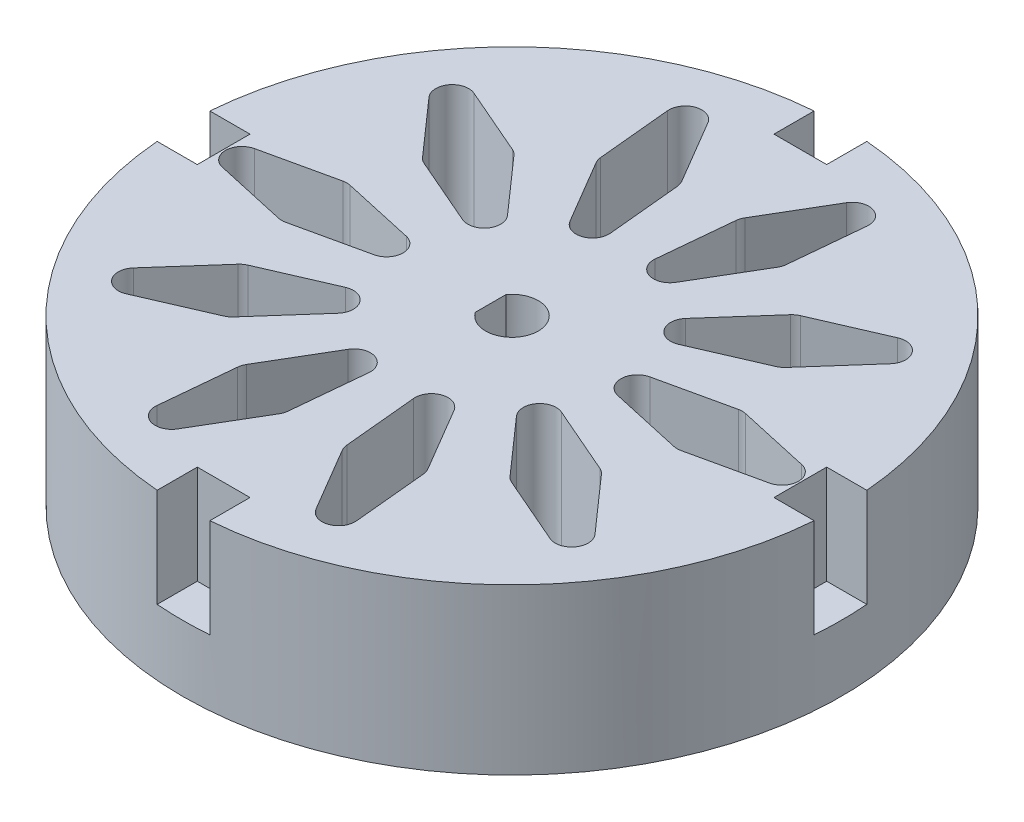
SolidWorks part; units mm, degrees
material "PET"
ref_plane "Спереди" through (0, 0, 0) normal (0, 0, 1) x (1, 0, 0)
ref_plane "Сверху" through (0, 0, 0) normal (0, 1, 0) x (1, 0, 0)
ref_plane "Справа" through (0, 0, 0) normal (1, 0, 0) x (0, 0, -1)
sketch "Эскиз1" plane through (0, 0, 0) normal (0, 1, 0) x (1, 0, 0)
  circle A0 centre (0, 0) radius 4
  circle A1 centre (0, 0) radius 20
  dimension "D1" = 8
  dimension "D2" = 40
extrude "Бобышка-Вытянуть1" add sketch "Эскиз1" along normal blind 10
sketch "Эскиз4" plane through (0, 0, 0) normal (0, -1, 0) x (1, 0, 0)
  circle A16 centre (0, 0) radius 20
  circle A32 centre (0, 0) radius 20
  dimension "D1" = 0
extrude "Бобышка-Вытянуть2" add sketch "Эскиз4" against normal blind 6
sketch "Эскиз5" plane through (0, 6, 0) normal (0, 1, 0) x (1, 0, 0)
  circle A0 centre (0, 0) radius 1.6
  dimension "D1" = 3.2
extrude "Вырез-Вытянуть2" cut sketch "Эскиз5" against normal through all both and the other way through all
sketch "Эскиз6" plane through (0, 0, 0) normal (0, -1, 0) x (1, 0, 0)
  line L0 (0, 0) -> (-3, 0) construction
  line L1 (-7.3928, 0.9762) -> (-11.7831, 1.9518)
  line L2 (-12.2169, 1.9518) -> (-16.6072, 0.9762)
  line L3 (-16.6072, -0.9762) -> (-12.2169, -1.9518)
  line L4 (-11.7831, -1.9518) -> (-7.3928, -0.9762)
  line L5 (-21, 0) -> (-3, 0) construction
  line L6 (-12, 2) -> (-12, -2) construction
  line L7 (-5.4071, 5.1352) -> (-8.3855, 8.5049)
  line L8 (-8.7365, 8.76) -> (-12.8617, 10.5512)
  line L9 (-14.0093, 8.9717) -> (-11.0309, 5.6019)
  line L10 (-10.6799, 5.3469) -> (-6.5547, 3.5557)
  line L11 (0, 0) -> (-2.4271, 1.7634) construction
  line L12 (-16.9894, 12.3435) -> (-2.4271, 1.7634) construction
  line L13 (-8.5326, 8.6715) -> (-10.8838, 5.4354) construction
  line L14 (-1.3561, 7.3327) -> (-1.7849, 11.8095)
  line L15 (-1.919, 12.2221) -> (-4.2035, 16.096)
  line L16 (-6.0603, 15.4927) -> (-5.6315, 11.0159)
  line L17 (-5.4974, 10.6032) -> (-3.2129, 6.7294)
  line L18 (0, 0) -> (-0.9271, 2.8532) construction
  line L19 (-6.4894, 19.9722) -> (-0.9271, 2.8532) construction
  line L20 (-1.8061, 12.0307) -> (-5.6103, 10.7946) construction
  line L21 (3.2129, 6.7294) -> (5.4974, 10.6032)
  line L22 (5.6315, 11.0159) -> (6.0603, 15.4927)
  line L23 (4.2035, 16.096) -> (1.919, 12.2221)
  line L24 (1.7849, 11.8095) -> (1.3561, 7.3327)
  line L25 (0, 0) -> (0.9271, 2.8532) construction
  line L26 (6.4894, 19.9722) -> (0.9271, 2.8532) construction
  line L27 (5.6103, 10.7946) -> (1.8061, 12.0307) construction
  line L28 (6.5547, 3.5557) -> (10.6799, 5.3469)
  line L29 (11.0309, 5.6019) -> (14.0093, 8.9717)
  line L30 (12.8617, 10.5512) -> (8.7365, 8.76)
  line L31 (8.3855, 8.5049) -> (5.4071, 5.1352)
  line L32 (0, 0) -> (2.4271, 1.7634) construction
  line L33 (16.9894, 12.3435) -> (2.4271, 1.7634) construction
  line L34 (10.8838, 5.4354) -> (8.5326, 8.6715) construction
  line L35 (7.3928, -0.9762) -> (11.7831, -1.9518)
  line L36 (12.2169, -1.9518) -> (16.6072, -0.9762)
  line L37 (16.6072, 0.9762) -> (12.2169, 1.9518)
  line L38 (11.7831, 1.9518) -> (7.3928, 0.9762)
  line L39 (0, 0) -> (3, 0) construction
  line L40 (21, 0) -> (3, 0) construction
  line L41 (12, -2) -> (12, 2) construction
  line L42 (5.4071, -5.1352) -> (8.3855, -8.5049)
  line L43 (8.7365, -8.76) -> (12.8617, -10.5512)
  line L44 (14.0093, -8.9717) -> (11.0309, -5.6019)
  line L45 (10.6799, -5.3469) -> (6.5547, -3.5557)
  line L46 (0, 0) -> (2.4271, -1.7634) construction
  line L47 (16.9894, -12.3435) -> (2.4271, -1.7634) construction
  line L48 (8.5326, -8.6715) -> (10.8838, -5.4354) construction
  line L49 (1.3561, -7.3327) -> (1.7849, -11.8095)
  line L50 (1.919, -12.2221) -> (4.2035, -16.096)
  line L51 (6.0603, -15.4927) -> (5.6315, -11.0159)
  line L52 (5.4974, -10.6032) -> (3.2129, -6.7294)
  line L53 (0, 0) -> (0.9271, -2.8532) construction
  line L54 (6.4894, -19.9722) -> (0.9271, -2.8532) construction
  line L55 (1.8061, -12.0307) -> (5.6103, -10.7946) construction
  line L56 (-3.2129, -6.7294) -> (-5.4974, -10.6032)
  line L57 (-5.6315, -11.0159) -> (-6.0603, -15.4927)
  line L58 (-4.2035, -16.096) -> (-1.919, -12.2221)
  line L59 (-1.7849, -11.8095) -> (-1.3561, -7.3327)
  line L60 (0, 0) -> (-0.9271, -2.8532) construction
  line L61 (-6.4894, -19.9722) -> (-0.9271, -2.8532) construction
  line L62 (-5.6103, -10.7946) -> (-1.8061, -12.0307) construction
  line L63 (-6.5547, -3.5557) -> (-10.6799, -5.3469)
  line L64 (-11.0309, -5.6019) -> (-14.0093, -8.9717)
  line L65 (-12.8617, -10.5512) -> (-8.7365, -8.76)
  line L66 (-8.3855, -8.5049) -> (-5.4071, -5.1352)
  line L67 (0, 0) -> (-2.4271, -1.7634) construction
  line L68 (-16.9894, -12.3435) -> (-2.4271, -1.7634) construction
  line L69 (-10.8838, -5.4354) -> (-8.5326, -8.6715) construction
  arc A0 (-12.2169, -1.9518) -> (-11.7831, -1.9518) centre (-12, -0.9756) ccw
  arc A1 (-7.3928, -0.9762) -> (-7.3928, 0.9762) centre (-7.6098, 0) ccw
  arc A2 (-11.7831, 1.9518) -> (-12.2169, 1.9518) centre (-12, 0.9756) ccw
  arc A3 (-16.6072, 0.9762) -> (-16.6072, -0.9762) centre (-16.3902, 0) ccw
  arc A4 (-11.0309, 5.6019) -> (-10.6799, 5.3469) centre (-10.2817, 6.2641) ccw
  arc A5 (-6.5547, 3.5557) -> (-5.4071, 5.1352) centre (-6.1564, 4.4729) ccw
  arc A6 (-8.3855, 8.5049) -> (-8.7365, 8.76) centre (-9.1348, 7.8427) ccw
  arc A7 (-12.8617, 10.5512) -> (-14.0093, 8.9717) centre (-13.26, 9.6339) ccw
  arc A8 (-5.6315, 11.0159) -> (-5.4974, 10.6032) centre (-4.6361, 11.1112) ccw
  arc A9 (-3.2129, 6.7294) -> (-1.3561, 7.3327) centre (-2.3515, 7.2373) ccw
  arc A10 (-1.7849, 11.8095) -> (-1.919, 12.2221) centre (-2.7803, 11.7142) ccw
  arc A11 (-4.2035, 16.096) -> (-6.0603, 15.4927) centre (-5.0649, 15.588) ccw
  arc A12 (1.919, 12.2221) -> (1.7849, 11.8095) centre (2.7803, 11.7142) ccw
  arc A13 (1.3561, 7.3327) -> (3.2129, 6.7294) centre (2.3515, 7.2373) ccw
  arc A14 (5.4974, 10.6032) -> (5.6315, 11.0159) centre (4.6361, 11.1112) ccw
  arc A15 (6.0603, 15.4927) -> (4.2035, 16.096) centre (5.0649, 15.588) ccw
  arc A16 (8.7365, 8.76) -> (8.3855, 8.5049) centre (9.1348, 7.8427) ccw
  arc A17 (5.4071, 5.1352) -> (6.5547, 3.5557) centre (6.1564, 4.4729) ccw
  arc A18 (10.6799, 5.3469) -> (11.0309, 5.6019) centre (10.2817, 6.2641) ccw
  arc A19 (14.0093, 8.9717) -> (12.8617, 10.5512) centre (13.26, 9.6339) ccw
  arc A20 (12.2169, 1.9518) -> (11.7831, 1.9518) centre (12, 0.9756) ccw
  arc A21 (7.3928, 0.9762) -> (7.3928, -0.9762) centre (7.6098, 0) ccw
  arc A22 (11.7831, -1.9518) -> (12.2169, -1.9518) centre (12, -0.9756) ccw
  arc A23 (16.6072, -0.9762) -> (16.6072, 0.9762) centre (16.3902, 0) ccw
  arc A24 (11.0309, -5.6019) -> (10.6799, -5.3469) centre (10.2817, -6.2641) ccw
  arc A25 (6.5547, -3.5557) -> (5.4071, -5.1352) centre (6.1564, -4.4729) ccw
  arc A26 (8.3855, -8.5049) -> (8.7365, -8.76) centre (9.1348, -7.8427) ccw
  arc A27 (12.8617, -10.5512) -> (14.0093, -8.9717) centre (13.26, -9.6339) ccw
  arc A28 (5.6315, -11.0159) -> (5.4974, -10.6032) centre (4.6361, -11.1112) ccw
  arc A29 (3.2129, -6.7294) -> (1.3561, -7.3327) centre (2.3515, -7.2373) ccw
  arc A30 (1.7849, -11.8095) -> (1.919, -12.2221) centre (2.7803, -11.7142) ccw
  arc A31 (4.2035, -16.096) -> (6.0603, -15.4927) centre (5.0649, -15.588) ccw
  arc A32 (-1.919, -12.2221) -> (-1.7849, -11.8095) centre (-2.7803, -11.7142) ccw
  arc A33 (-1.3561, -7.3327) -> (-3.2129, -6.7294) centre (-2.3515, -7.2373) ccw
  arc A34 (-5.4974, -10.6032) -> (-5.6315, -11.0159) centre (-4.6361, -11.1112) ccw
  arc A35 (-6.0603, -15.4927) -> (-4.2035, -16.096) centre (-5.0649, -15.588) ccw
  arc A36 (-8.7365, -8.76) -> (-8.3855, -8.5049) centre (-9.1348, -7.8427) ccw
  arc A37 (-5.4071, -5.1352) -> (-6.5547, -3.5557) centre (-6.1564, -4.4729) ccw
  arc A38 (-10.6799, -5.3469) -> (-11.0309, -5.6019) centre (-10.2817, -6.2641) ccw
  arc A39 (-14.0093, -8.9717) -> (-12.8617, -10.5512) centre (-13.26, -9.6339) ccw
  point P3 (-12, 0)
  point P21 (9.7082, -7.0534)
  point P23 (-9.7082, 7.0534)
  point P40 (-3.7082, 11.4127)
  point P57 (3.7082, 11.4127)
  point P74 (9.7082, 7.0534)
  point P91 (12, 0)
  point P107 (0, 0)
  point P123 (3.7082, -11.4127)
  point P140 (-3.7082, -11.4127)
  point P157 (-9.7082, -7.0534)
  dimension "D4" = 1
  dimension "D1" = 4
  dimension "D2" = 18
  dimension "D3" = 3
  dimension "D5" = 10
extrude "Вырез-Вытянуть3" cut sketch "Эскиз6" against normal through all both and the other way through all
sketch "Эскиз8" plane through (0, 10, 0) normal (0, 1, 0) x (1, 0, 0)
  line L0 (0, 0) -> (-20, 0) construction
  line L1 (1.6, 17.5) -> (1.6, 22.5)
  line L2 (-17.5, 1.6) -> (-22.5, 1.6)
  line L3 (-17.5, 1.6) -> (-17.5, -1.6)
  line L4 (-17.5, -1.6) -> (-22.5, -1.6)
  line L5 (-22.5, 1.6) -> (-22.5, -1.6)
  line L6 (-17.5, 1.6) -> (-22.5, -1.6) construction
  line L7 (-17.5, -1.6) -> (-22.5, 1.6) construction
  line L8 (1.6, 17.5) -> (-1.6, 17.5)
  line L9 (-1.6, 17.5) -> (-1.6, 22.5)
  line L10 (1.6, 22.5) -> (-1.6, 22.5)
  line L11 (0, 0) -> (0, 20) construction
  line L12 (1.6, 17.5) -> (-1.6, 22.5) construction
  line L13 (-1.6, 17.5) -> (1.6, 22.5) construction
  line L14 (17.5, -1.6) -> (22.5, -1.6)
  line L15 (17.5, -1.6) -> (17.5, 1.6)
  line L16 (17.5, 1.6) -> (22.5, 1.6)
  line L17 (22.5, -1.6) -> (22.5, 1.6)
  line L18 (0, 0) -> (20, 0) construction
  line L19 (17.5, -1.6) -> (22.5, 1.6) construction
  line L20 (17.5, 1.6) -> (22.5, -1.6) construction
  line L21 (-1.6, -17.5) -> (-1.6, -22.5)
  line L22 (-1.6, -17.5) -> (1.6, -17.5)
  line L23 (1.6, -17.5) -> (1.6, -22.5)
  line L24 (-1.6, -22.5) -> (1.6, -22.5)
  line L25 (0, 0) -> (0, -20) construction
  line L26 (-1.6, -17.5) -> (1.6, -22.5) construction
  line L27 (1.6, -17.5) -> (-1.6, -22.5) construction
  circle A0 centre (0, 0) radius 20 construction
  point P28 (0, 0)
  dimension "D1" = 3.2
  dimension "D2" = 5
  dimension "D3" = 4
extrude "Вырез-Вытянуть4" cut sketch "Эскиз8" against normal blind 6
sketch "Эскиз9" plane through (0, 0, 0) normal (0, -1, 0) x (1, 0, 0)
  circle A0 centre (0, 0) radius 3
  dimension "D1" = 6
extrude "Вырез-Вытянуть5" cut sketch "Эскиз9" against normal blind 2
sketch "Эскиз11" plane through (0, 6, 0) normal (0, 1, 0) x (1, 0, 0)
  line L0 (-1.3, 0.9327) -> (-1.3, -0.9327)
  arc A0 (-1.3, -0.9327) -> (-1.3, 0.9327) centre (0, 0) ccw
  circle A2 centre (0, 0) radius 4
  circle A3 centre (0, 0) radius 4
  dimension "D1" = 3.2
  dimension "D2" = 1.3
  dimension "D3" = 0
extrude "Бобышка-Вытянуть3" add sketch "Эскиз11" along normal up to surface (4 mm away) up to face at (0, 10, 0)
sketch "Эскиз12" plane through (0, 2, 0) normal (0, -1, 0) x (1, 0, 0)
  circle A1 centre (0, 0) radius 3
  circle A2 centre (0, 0) radius 3
  dimension "D1" = 0
extrude "Бобышка-Вытянуть4" add sketch "Эскиз12" along normal up to surface (2 mm away) up to face at (0, 0, -3)
sketch "Эскиз13" plane through (0, 2, 0) normal (0, 1, 0) x (1, 0, 0)
  circle A1 centre (0, 0) radius 1.6
  circle A2 centre (0, 0) radius 1.6
  dimension "D1" = 0
extrude "Бобышка-Вытянуть5" add sketch "Эскиз13" along normal blind 2
